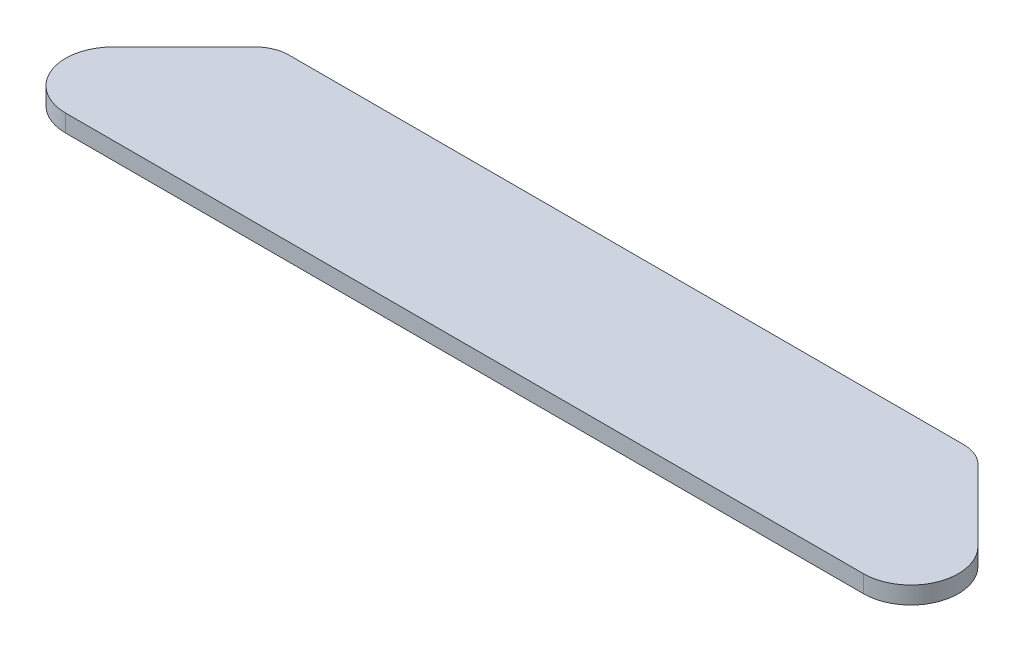
SolidWorks part; units mm, degrees
ref_plane "Front Plane" through (0, 0, 0) normal (0, 0, 1) x (1, 0, 0)
ref_plane "Top Plane" through (0, 0, 0) normal (0, 1, 0) x (1, 0, 0)
ref_plane "Right Plane" through (0, 0, 0) normal (1, 0, 0) x (0, 0, -1)
sketch "Sketch1" plane through (0, 0, 0) normal (0, 1, 0) x (1, 0, 0)
  line L0 (-1003.2092, 19.5741) -> (-852.0418, 170.7415)
  line L1 (-927.775, -162.54) -> (812.2792, -162.54)
  line L2 (812.2792, -162.54) -> (818.4113, -162.54)
  line L4 (-927.775, -162.54) -> (-933.9071, -162.54)
  line L6 (-752.4659, 193.06) -> (636.9701, 193.06)
  line L7 (636.9701, 193.06) -> (682.6644, 193.06)
  line L8 (-752.4659, 193.06) -> (-799.2123, 193.06)
  line L9 (-852.0418, 170.7415) -> (-851.2978, 171.4855)
  line L10 (892.0494, 15.2381) -> (736.546, 170.7415)
  line L11 (-1007.5452, 15.2381) -> (-1003.2092, 19.5741)
  arc A0 (-933.9071, -162.54) -> (-1007.5452, 15.2381) centre (-933.9071, -58.4) cw
  arc A1 (892.0494, 15.2381) -> (818.4113, -162.54) centre (818.4113, -58.4) cw
  arc A2 (682.6644, 193.06) -> (736.546, 170.7415) centre (682.6644, 116.86) cw
  arc A3 (-851.2978, 171.4855) -> (-799.2123, 193.06) centre (-799.2123, 119.4) cw
  dimension "D1" = 104.14
  dimension "D2" = 104.14
  dimension "D3" = 76.2
  dimension "D4" = 73.66
extrude "Boss-Extrude1" add sketch "Sketch1" along normal blind 38.1
sketch "Sketch2" plane through (0, 0, 0) normal (0, -1, 0) x (1, 0, 0)
  circle A0 centre (-629.1071, 58.4) radius 12.7
  circle A1 centre (513.6113, 58.4) radius 12.7
  dimension "D2" = 25.4
  dimension "D4" = 25.4
  dimension "D1" = 0
  dimension "D3" = 304.8
  dimension "D5" = 304.8
extrude "Cut-Extrude1" cut sketch "Sketch2" against normal blind 12.7
